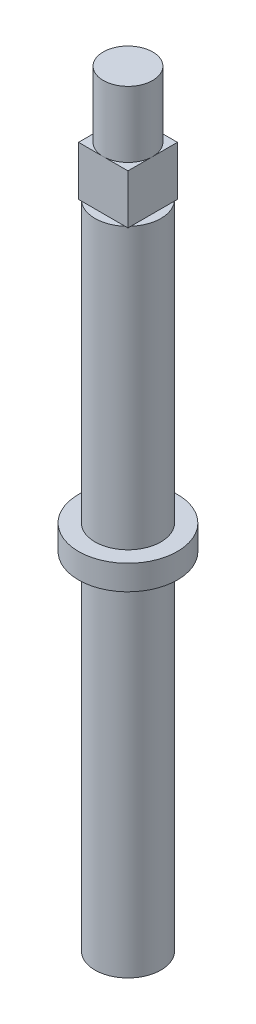
SolidWorks part; units mm, degrees
ref_plane "Front Plane" through (0, 0, 0) normal (0, 0, 1) x (1, 0, 0)
ref_plane "Top Plane" through (0, 0, 0) normal (0, 1, 0) x (1, 0, 0)
ref_plane "Right Plane" through (0, 0, 0) normal (1, 0, 0) x (0, 0, -1)
sketch "Sketch1" plane through (0, 0, 0) normal (1, 0, 0) x (0, 0, -1)
  line L0 (0, 46.5) -> (0, -46.5) construction
  line L1 (0, 46.5) -> (3, 46.5)
  line L2 (3, 46.5) -> (3, 32.5)
  line L3 (3, 32.5) -> (4, 32.5)
  line L4 (4, 32.5) -> (4, -1.5)
  line L5 (4, -1.5) -> (6, -1.5)
  line L6 (6, -1.5) -> (6, -4.5)
  line L7 (6, -4.5) -> (4, -4.5)
  line L8 (4, -4.5) -> (4, -46.5)
  line L9 (4, -46.5) -> (0, -46.5)
  line L10 (0, -46.5) -> (0, 46.5)
  dimension "D1" = 93
  dimension "D2" = 3
  dimension "D3" = 34
  dimension "D4" = 3
  dimension "D5" = 4
  dimension "D6" = 42
  dimension "D7" = 4
  dimension "D8" = 6
revolve "Revolve1" add sketch "Sketch1" angle 360 about L0
sketch "Sketch2" plane through (0, 32.5, 0) normal (0, 1, 0) x (1, 0, 0)
  line L1 (-3, -3) -> (3, -3)
  line L2 (-3, -3) -> (-3, 3)
  line L3 (-3, 3) -> (3, 3)
  line L4 (3, -3) -> (3, 3)
  line L5 (-3, -3) -> (3, 3) construction
  line L6 (-3, 3) -> (3, -3) construction
  point P0 (0, 0)
  dimension "D1" = 6
  dimension "D2" = 6
extrude "Boss-Extrude1" add sketch "Sketch2" along normal blind 6
